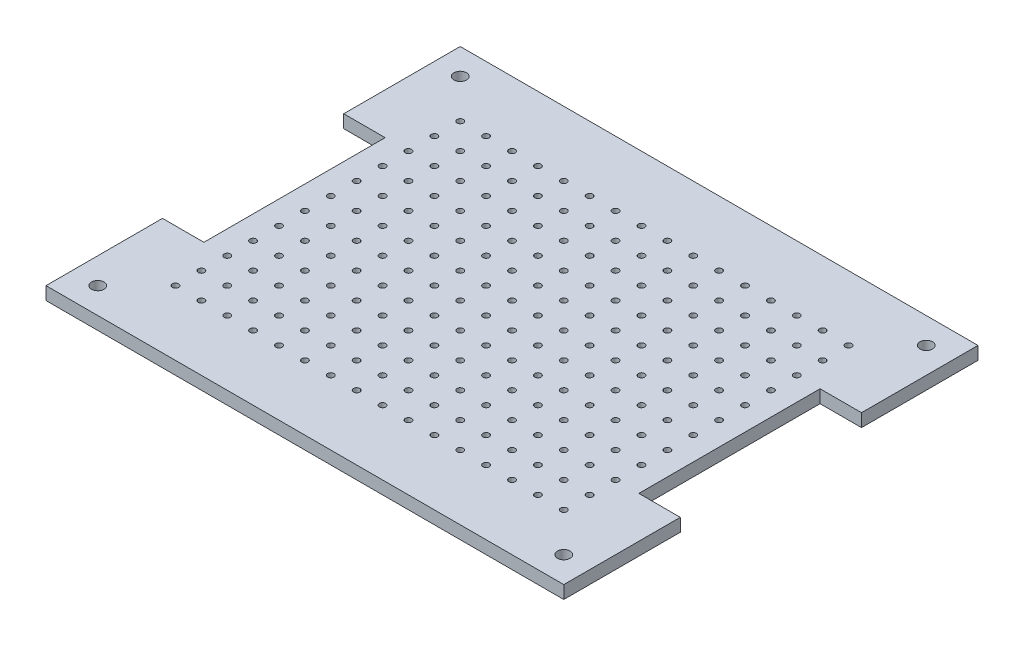
SolidWorks part; units mm, degrees
ref_plane "Front Plane" through (0, 0, 0) normal (0, 0, 1) x (1, 0, 0)
ref_plane "Top Plane" through (0, 0, 0) normal (0, 1, 0) x (1, 0, 0)
ref_plane "Right Plane" through (0, 0, 0) normal (1, 0, 0) x (0, 0, -1)
sketch "Sketch1" plane through (0, 0, 0) normal (0, 1, 0) x (1, 0, 0)
  line L0 (0, 101.6) -> (50000, 101.6) construction
  line L1 (0, 0) -> (254, 0)
  line L2 (0, 0) -> (0, 57.15)
  line L3 (0, 203.2) -> (254, 203.2)
  line L4 (254, 0) -> (254, 57.15)
  line L5 (254, 57.15) -> (233.68, 57.15)
  line L7 (254, 146.05) -> (233.68, 146.05)
  line L8 (233.68, 57.15) -> (233.68, 146.05)
  line L9 (254, 146.05) -> (254, 203.2)
  line L10 (0, 146.05) -> (0, 203.2)
  line L11 (0, 146.05) -> (20.32, 146.05)
  line L13 (0, 57.15) -> (20.32, 57.15)
  line L14 (20.32, 146.05) -> (20.32, 57.15)
  line L16 (25.4, 177.8) -> (228.6, 177.8) construction
  line L17 (25.4, 177.8) -> (25.4, 25.4) construction
  line L18 (25.4, 25.4) -> (228.6, 25.4) construction
  line L19 (228.6, 177.8) -> (228.6, 25.4) construction
  line L20 (12.7, 190.5) -> (241.3, 190.5) construction
  line L21 (12.7, 190.5) -> (12.7, 12.7) construction
  line L22 (12.7, 12.7) -> (241.3, 12.7) construction
  line L23 (241.3, 190.5) -> (241.3, 12.7) construction
  line L24 (31.75, 171.45) -> (222.25, 171.45) construction
  line L25 (31.75, 171.45) -> (31.75, 31.75) construction
  line L26 (31.75, 31.75) -> (222.25, 31.75) construction
  line L27 (222.25, 171.45) -> (222.25, 31.75) construction
  circle A0 centre (31.75, 171.45) radius 1.55
  circle A1 centre (44.45, 171.45) radius 1.55
  circle A2 centre (57.15, 171.45) radius 1.55
  circle A3 centre (69.85, 171.45) radius 1.55
  circle A4 centre (82.55, 171.45) radius 1.55
  circle A5 centre (95.25, 171.45) radius 1.55
  circle A6 centre (107.95, 171.45) radius 1.55
  circle A7 centre (120.65, 171.45) radius 1.55
  circle A8 centre (133.35, 171.45) radius 1.55
  circle A9 centre (146.05, 171.45) radius 1.55
  circle A10 centre (158.75, 171.45) radius 1.55
  circle A11 centre (171.45, 171.45) radius 1.55
  circle A12 centre (184.15, 171.45) radius 1.55
  circle A13 centre (196.85, 171.45) radius 1.55
  circle A14 centre (209.55, 171.45) radius 1.55
  circle A15 centre (222.25, 171.45) radius 1.55
  circle A16 centre (44.45, 158.75) radius 1.55
  circle A17 centre (57.15, 158.75) radius 1.55
  circle A18 centre (69.85, 158.75) radius 1.55
  circle A19 centre (82.55, 158.75) radius 1.55
  circle A20 centre (95.25, 158.75) radius 1.55
  circle A21 centre (107.95, 158.75) radius 1.55
  circle A22 centre (120.65, 158.75) radius 1.55
  circle A23 centre (133.35, 158.75) radius 1.55
  circle A24 centre (146.05, 158.75) radius 1.55
  circle A25 centre (158.75, 158.75) radius 1.55
  circle A26 centre (171.45, 158.75) radius 1.55
  circle A27 centre (184.15, 158.75) radius 1.55
  circle A28 centre (196.85, 158.75) radius 1.55
  circle A29 centre (209.55, 158.75) radius 1.55
  circle A30 centre (222.25, 158.75) radius 1.55
  circle A31 centre (44.45, 146.05) radius 1.55
  circle A32 centre (57.15, 146.05) radius 1.55
  circle A33 centre (69.85, 146.05) radius 1.55
  circle A34 centre (82.55, 146.05) radius 1.55
  circle A35 centre (95.25, 146.05) radius 1.55
  circle A36 centre (107.95, 146.05) radius 1.55
  circle A37 centre (120.65, 146.05) radius 1.55
  circle A38 centre (133.35, 146.05) radius 1.55
  circle A39 centre (146.05, 146.05) radius 1.55
  circle A40 centre (158.75, 146.05) radius 1.55
  circle A41 centre (171.45, 146.05) radius 1.55
  circle A42 centre (184.15, 146.05) radius 1.55
  circle A43 centre (196.85, 146.05) radius 1.55
  circle A44 centre (209.55, 146.05) radius 1.55
  circle A45 centre (222.25, 146.05) radius 1.55
  circle A46 centre (44.45, 133.35) radius 1.55
  circle A47 centre (57.15, 133.35) radius 1.55
  circle A48 centre (69.85, 133.35) radius 1.55
  circle A49 centre (82.55, 133.35) radius 1.55
  circle A50 centre (95.25, 133.35) radius 1.55
  circle A51 centre (107.95, 133.35) radius 1.55
  circle A52 centre (120.65, 133.35) radius 1.55
  circle A53 centre (133.35, 133.35) radius 1.55
  circle A54 centre (146.05, 133.35) radius 1.55
  circle A55 centre (158.75, 133.35) radius 1.55
  circle A56 centre (171.45, 133.35) radius 1.55
  circle A57 centre (184.15, 133.35) radius 1.55
  circle A58 centre (196.85, 133.35) radius 1.55
  circle A59 centre (209.55, 133.35) radius 1.55
  circle A60 centre (222.25, 133.35) radius 1.55
  circle A61 centre (44.45, 120.65) radius 1.55
  circle A62 centre (57.15, 120.65) radius 1.55
  circle A63 centre (69.85, 120.65) radius 1.55
  circle A64 centre (82.55, 120.65) radius 1.55
  circle A65 centre (95.25, 120.65) radius 1.55
  circle A66 centre (107.95, 120.65) radius 1.55
  circle A67 centre (120.65, 120.65) radius 1.55
  circle A68 centre (133.35, 120.65) radius 1.55
  circle A69 centre (146.05, 120.65) radius 1.55
  circle A70 centre (158.75, 120.65) radius 1.55
  circle A71 centre (171.45, 120.65) radius 1.55
  circle A72 centre (184.15, 120.65) radius 1.55
  circle A73 centre (196.85, 120.65) radius 1.55
  circle A74 centre (209.55, 120.65) radius 1.55
  circle A75 centre (222.25, 120.65) radius 1.55
  circle A76 centre (44.45, 107.95) radius 1.55
  circle A77 centre (57.15, 107.95) radius 1.55
  circle A78 centre (69.85, 107.95) radius 1.55
  circle A79 centre (82.55, 107.95) radius 1.55
  circle A80 centre (95.25, 107.95) radius 1.55
  circle A81 centre (107.95, 107.95) radius 1.55
  circle A82 centre (120.65, 107.95) radius 1.55
  circle A83 centre (133.35, 107.95) radius 1.55
  circle A84 centre (146.05, 107.95) radius 1.55
  circle A85 centre (158.75, 107.95) radius 1.55
  circle A86 centre (171.45, 107.95) radius 1.55
  circle A87 centre (184.15, 107.95) radius 1.55
  circle A88 centre (196.85, 107.95) radius 1.55
  circle A89 centre (209.55, 107.95) radius 1.55
  circle A90 centre (222.25, 107.95) radius 1.55
  circle A91 centre (44.45, 95.25) radius 1.55
  circle A92 centre (57.15, 95.25) radius 1.55
  circle A93 centre (69.85, 95.25) radius 1.55
  circle A94 centre (82.55, 95.25) radius 1.55
  circle A95 centre (95.25, 95.25) radius 1.55
  circle A96 centre (107.95, 95.25) radius 1.55
  circle A97 centre (120.65, 95.25) radius 1.55
  circle A98 centre (133.35, 95.25) radius 1.55
  circle A99 centre (146.05, 95.25) radius 1.55
  circle A100 centre (158.75, 95.25) radius 1.55
  circle A101 centre (171.45, 95.25) radius 1.55
  circle A102 centre (184.15, 95.25) radius 1.55
  circle A103 centre (196.85, 95.25) radius 1.55
  circle A104 centre (209.55, 95.25) radius 1.55
  circle A105 centre (222.25, 95.25) radius 1.55
  circle A106 centre (44.45, 82.55) radius 1.55
  circle A107 centre (57.15, 82.55) radius 1.55
  circle A108 centre (69.85, 82.55) radius 1.55
  circle A109 centre (82.55, 82.55) radius 1.55
  circle A110 centre (95.25, 82.55) radius 1.55
  circle A111 centre (107.95, 82.55) radius 1.55
  circle A112 centre (120.65, 82.55) radius 1.55
  circle A113 centre (133.35, 82.55) radius 1.55
  circle A114 centre (146.05, 82.55) radius 1.55
  circle A115 centre (158.75, 82.55) radius 1.55
  circle A116 centre (171.45, 82.55) radius 1.55
  circle A117 centre (184.15, 82.55) radius 1.55
  circle A118 centre (196.85, 82.55) radius 1.55
  circle A119 centre (209.55, 82.55) radius 1.55
  circle A120 centre (222.25, 82.55) radius 1.55
  circle A121 centre (44.45, 69.85) radius 1.55
  circle A122 centre (57.15, 69.85) radius 1.55
  circle A123 centre (69.85, 69.85) radius 1.55
  circle A124 centre (82.55, 69.85) radius 1.55
  circle A125 centre (95.25, 69.85) radius 1.55
  circle A126 centre (107.95, 69.85) radius 1.55
  circle A127 centre (120.65, 69.85) radius 1.55
  circle A128 centre (133.35, 69.85) radius 1.55
  circle A129 centre (146.05, 69.85) radius 1.55
  circle A130 centre (158.75, 69.85) radius 1.55
  circle A131 centre (171.45, 69.85) radius 1.55
  circle A132 centre (184.15, 69.85) radius 1.55
  circle A133 centre (196.85, 69.85) radius 1.55
  circle A134 centre (209.55, 69.85) radius 1.55
  circle A135 centre (222.25, 69.85) radius 1.55
  circle A136 centre (44.45, 57.15) radius 1.55
  circle A137 centre (57.15, 57.15) radius 1.55
  circle A138 centre (69.85, 57.15) radius 1.55
  circle A139 centre (82.55, 57.15) radius 1.55
  circle A140 centre (95.25, 57.15) radius 1.55
  circle A141 centre (107.95, 57.15) radius 1.55
  circle A142 centre (120.65, 57.15) radius 1.55
  circle A143 centre (133.35, 57.15) radius 1.55
  circle A144 centre (146.05, 57.15) radius 1.55
  circle A145 centre (158.75, 57.15) radius 1.55
  circle A146 centre (171.45, 57.15) radius 1.55
  circle A147 centre (184.15, 57.15) radius 1.55
  circle A148 centre (196.85, 57.15) radius 1.55
  circle A149 centre (209.55, 57.15) radius 1.55
  circle A150 centre (222.25, 57.15) radius 1.55
  circle A151 centre (44.45, 44.45) radius 1.55
  circle A152 centre (57.15, 44.45) radius 1.55
  circle A153 centre (69.85, 44.45) radius 1.55
  circle A154 centre (82.55, 44.45) radius 1.55
  circle A155 centre (95.25, 44.45) radius 1.55
  circle A156 centre (107.95, 44.45) radius 1.55
  circle A157 centre (120.65, 44.45) radius 1.55
  circle A158 centre (133.35, 44.45) radius 1.55
  circle A159 centre (146.05, 44.45) radius 1.55
  circle A160 centre (158.75, 44.45) radius 1.55
  circle A161 centre (171.45, 44.45) radius 1.55
  circle A162 centre (184.15, 44.45) radius 1.55
  circle A163 centre (196.85, 44.45) radius 1.55
  circle A164 centre (209.55, 44.45) radius 1.55
  circle A165 centre (222.25, 44.45) radius 1.55
  circle A166 centre (44.45, 31.75) radius 1.55
  circle A167 centre (57.15, 31.75) radius 1.55
  circle A168 centre (69.85, 31.75) radius 1.55
  circle A169 centre (82.55, 31.75) radius 1.55
  circle A170 centre (95.25, 31.75) radius 1.55
  circle A171 centre (107.95, 31.75) radius 1.55
  circle A172 centre (120.65, 31.75) radius 1.55
  circle A173 centre (133.35, 31.75) radius 1.55
  circle A174 centre (146.05, 31.75) radius 1.55
  circle A175 centre (158.75, 31.75) radius 1.55
  circle A176 centre (171.45, 31.75) radius 1.55
  circle A177 centre (184.15, 31.75) radius 1.55
  circle A178 centre (196.85, 31.75) radius 1.55
  circle A179 centre (209.55, 31.75) radius 1.55
  circle A180 centre (222.25, 31.75) radius 1.55
  circle A181 centre (31.75, 158.75) radius 1.55
  circle A182 centre (31.75, 146.05) radius 1.55
  circle A183 centre (31.75, 133.35) radius 1.55
  circle A184 centre (31.75, 120.65) radius 1.55
  circle A185 centre (31.75, 107.95) radius 1.55
  circle A186 centre (31.75, 95.25) radius 1.55
  circle A187 centre (31.75, 82.55) radius 1.55
  circle A188 centre (31.75, 69.85) radius 1.55
  circle A189 centre (31.75, 57.15) radius 1.55
  circle A190 centre (31.75, 44.45) radius 1.55
  circle A191 centre (31.75, 31.75) radius 1.55
  circle A192 centre (12.7, 190.5) radius 3.1
  circle A193 centre (241.3, 190.5) radius 3.1
  circle A194 centre (241.3, 12.7) radius 3.1
  circle A195 centre (12.7, 12.7) radius 3.1
  dimension "D22" = 3.1
  dimension "D25" = 6.2
  dimension "D26" = 6.2
  dimension "D27" = 6.2
  dimension "D28" = 6.2
  dimension "D1" = 203.2
  dimension "D2" = 254
  dimension "D3" = 20.32
  dimension "D4" = 20.32
  dimension "D5" = 44.45
  dimension "D6" = 101.6
  dimension "D7" = 44.45
  dimension "D8" = 44.45
  dimension "D9" = 44.45
  dimension "D10" = 25.4
  dimension "D11" = 25.4
  dimension "D12" = 25.4
  dimension "D13" = 25.4
  dimension "D14" = 12.7
  dimension "D15" = 12.7
  dimension "D16" = 12.7
  dimension "D17" = 12.7
  dimension "D18" = 6.35
  dimension "D19" = 6.35
  dimension "D20" = 6.35
  dimension "D21" = 6.35
  dimension "D23" = 16
  dimension "D24" = 12
extrude "Boss-Extrude1" add sketch "Sketch1" along normal blind 6.35
